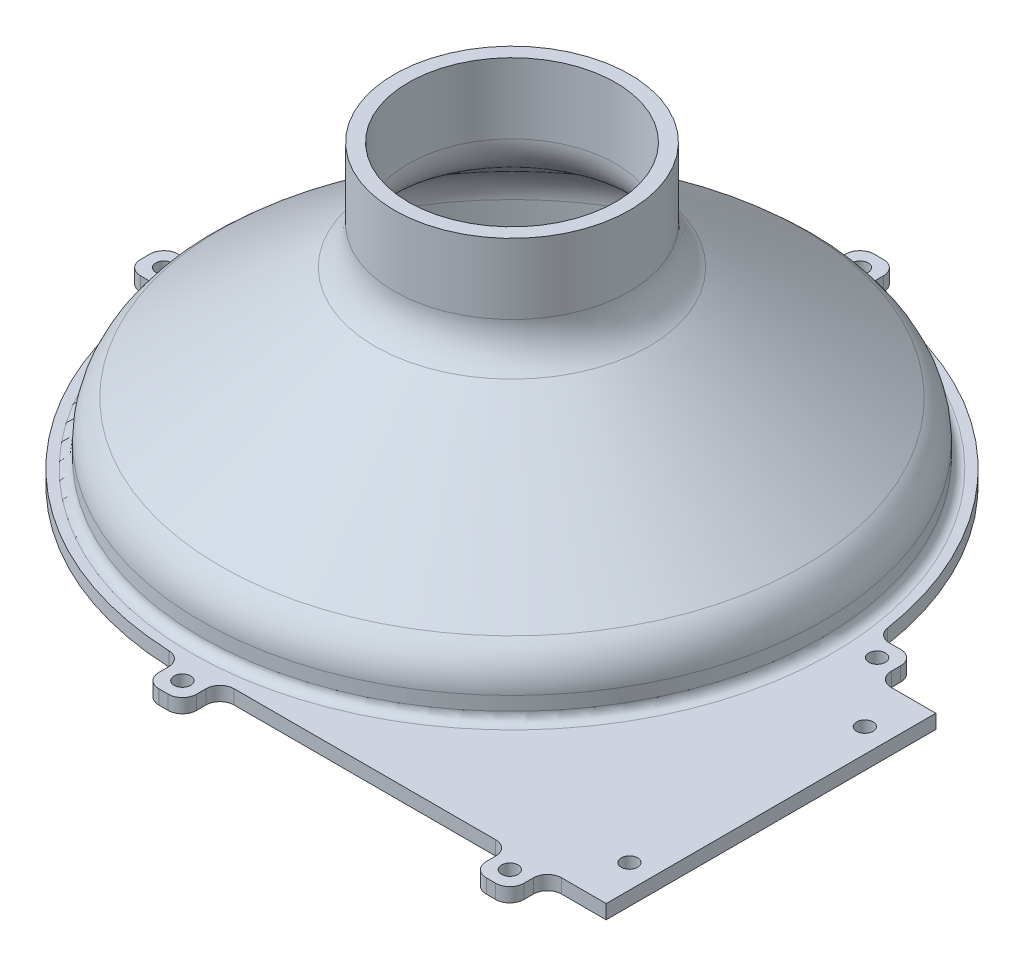
SolidWorks part; units mm, degrees
ref_plane "Front Plane" through (0, 0, 0) normal (0, 0, 1) x (1, 0, 0)
ref_plane "Top Plane" through (0, 0, 0) normal (0, 1, 0) x (1, 0, 0)
ref_plane "Right Plane" through (0, 0, 0) normal (1, 0, 0) x (0, 0, -1)
sketch "Sketch2" plane through (0, 0, 0) normal (0, 1, 0) x (1, 0, 0)
  line L0 (70, 0) -> (70, -70) construction
  line L1 (0, -70) -> (90, -70)
  line L3 (70, 0) -> (90, 0)
  line L4 (90, -70) -> (90, 0)
  arc A0 (70, 0) -> (0, -70) centre (0, 0) ccw
  circle A1 centre (0, 0) radius 63
  dimension "D1" = 140
  dimension "D4" = 126
  dimension "D3" = 20
extrude "Boss-Extrude1" add sketch "Sketch2" along normal blind 3
sketch "Sketch3" plane through (0, 3, 0) normal (0, 1, 0) x (1, 0, 0)
  circle A2 centre (0, 0) radius 63 construction
  circle A3 centre (0, 0) radius 63
  circle A4 centre (0, 0) radius 66
  dimension "D1" = 3
extrude "Boss-Extrude2" add sketch "Sketch3" along normal blind 10
sketch "Sketch6" plane through (0, 0, 0) normal (1, 0, 0) x (0, 0, -1)
  line L0 (-66, 13) -> (-25, 43)
  line L1 (-25, 43) -> (-22, 43)
  line L2 (-22, 43) -> (-63, 13)
  line L3 (66, 13) -> (-66, 13) construction
  line L4 (-66, 13) -> (-63, 13)
  line L5 (0, 0) -> (0, 43) construction
  line L6 (-70, 0) -> (70, 0) construction
  line L7 (-22, 43) -> (0, 43) construction
  dimension "D1" = 3
  dimension "D2" = 30
  dimension "D3" = 25
revolve "Revolve1" add sketch "Sketch6" angle 360 about L5
sketch "Sketch7" plane through (0, 43, 0) normal (0, 1, 0) x (1, 0, 0)
  circle A0 centre (0, 0) radius 25
  circle A1 centre (0, 0) radius 22
  circle A2 centre (0, 0) radius 22 construction
  circle A3 centre (0, 0) radius 25 construction
extrude "Boss-Extrude3" add sketch "Sketch7" along normal blind 20
fillet "Fillet1" radius 10 4 edges at (0, 43, -22) (0, 13, -63) (0, 13, 66) (0, 43, 25)
fillet "Fillet2" radius 2 1 edges at (0, 3, 66)
sketch "Sketch8" plane through (0, 0, 0) normal (0, -1, 0) x (1, 0, 0)
  line L21 (90, 0) -> (70, 0) construction
  line L22 (77.5414, 0) -> (69.5414, 0)
  line L23 (77.5414, 0) -> (77.5414, -8)
  line L24 (77.5414, -8) -> (69.5414, -8)
  line L25 (69.5414, 0) -> (69.5414, -8)
  line L26 (73.5414, 0) -> (73.5414, -8) construction
  line L27 (0, 70) -> (90, 70) construction
  line L28 (77.5414, 70) -> (69.5414, 70)
  line L29 (77.5414, 70) -> (77.5414, 78)
  line L30 (77.5414, 78) -> (69.5414, 78)
  line L31 (69.5414, 70) -> (69.5414, 78)
  line L32 (73.5414, 78) -> (73.5414, 70) construction
  line L33 (-73.8856, 4) -> (-73.8856, -4) construction
  line L34 (-69.8856, 4) -> (-77.8856, 4)
  line L35 (-69.8856, 4) -> (-69.8856, -4)
  line L36 (-69.8856, -4) -> (-77.8856, -4)
  line L37 (-77.8856, 4) -> (-77.8856, -4)
  line L38 (0, -69.8856) -> (0, -77.8856) construction
  line L39 (-4, -69.8856) -> (4, -69.8856)
  line L40 (-4, -69.8856) -> (-4, -77.8856)
  line L41 (-4, -77.8856) -> (4, -77.8856)
  line L42 (4, -69.8856) -> (4, -77.8856)
  line L43 (4, 78) -> (4, 70) construction
  line L44 (0, 70) -> (8, 70)
  line L45 (0, 70) -> (0, 78)
  line L46 (0, 78) -> (8, 78)
  line L47 (8, 70) -> (8, 78)
  arc A23 (0, 70) -> (70, 0) centre (0, 0) ccw construction
  circle A24 centre (73.5414, -4) radius 1.75
  circle A25 centre (73.5414, 74) radius 1.75
  circle A26 centre (-73.8856, 0) radius 1.75
  circle A27 centre (0, -73.8856) radius 1.75
  circle A28 centre (4, 74) radius 1.75
  dimension "D3" = 3.5
  dimension "D5" = 3.5
  dimension "D8" = 3.5
  dimension "D11" = 3.5
  dimension "D13" = 3.5
  dimension "D1" = 8
  dimension "D2" = 8
  dimension "D4" = 8
  dimension "D6" = 8
  dimension "D7" = 8
  dimension "D9" = 8
  dimension "D10" = 8
  dimension "D12" = 8
extrude "Boss-Extrude4" add sketch "Sketch8" against normal up to surface (3 mm away) up to face at (0, 3, 68)
fillet "Fillet3" radius 3 19 edges at (77.5414, 1.5, 0) (69.5414, 1.5, -8) (77.5414, 1.5, -8) (77.5414, 1.5, 70) (77.5414, 1.5, 78) (69.5414, 1.5, 78) (69.5414, 1.5, 70) (8, 1.5, 70) (8, 1.5, 78) (0, 1.5, 78) (0, 1.5, 70) (-69.8856, 1.5, 4) (-77.8856, 1.5, 4) (-77.8856, 1.5, -4) (-69.8856, 1.5, -4) (-4, 1.5, -77.8856) (4, 1.5, -77.8856) (4, 1.5, -69.8856) (-4, 1.5, -69.8856)
sketch "Sketch9" plane through (0, 3, 0) normal (0, 1, 0) x (1, 0, 0)
  line L0 (84.93, 0) -> (84.93, -70) construction
  line L1 (90, 0) -> (80.5414, 0) construction
  line L2 (80.5414, -70) -> (90, -70) construction
  line L3 (90, -70) -> (90, 0) construction
  circle A0 centre (84.93, -10) radius 1.75
  circle A1 centre (84.93, -60) radius 1.75
  dimension "D2" = 3.5
  dimension "D3" = 3.5
  dimension "D1" = 5.07
  dimension "D4" = 10
  dimension "D5" = 10
extrude "Cut-Extrude1" cut sketch "Sketch9" against normal through all
equation "\"LoftHeight\"= 30"
